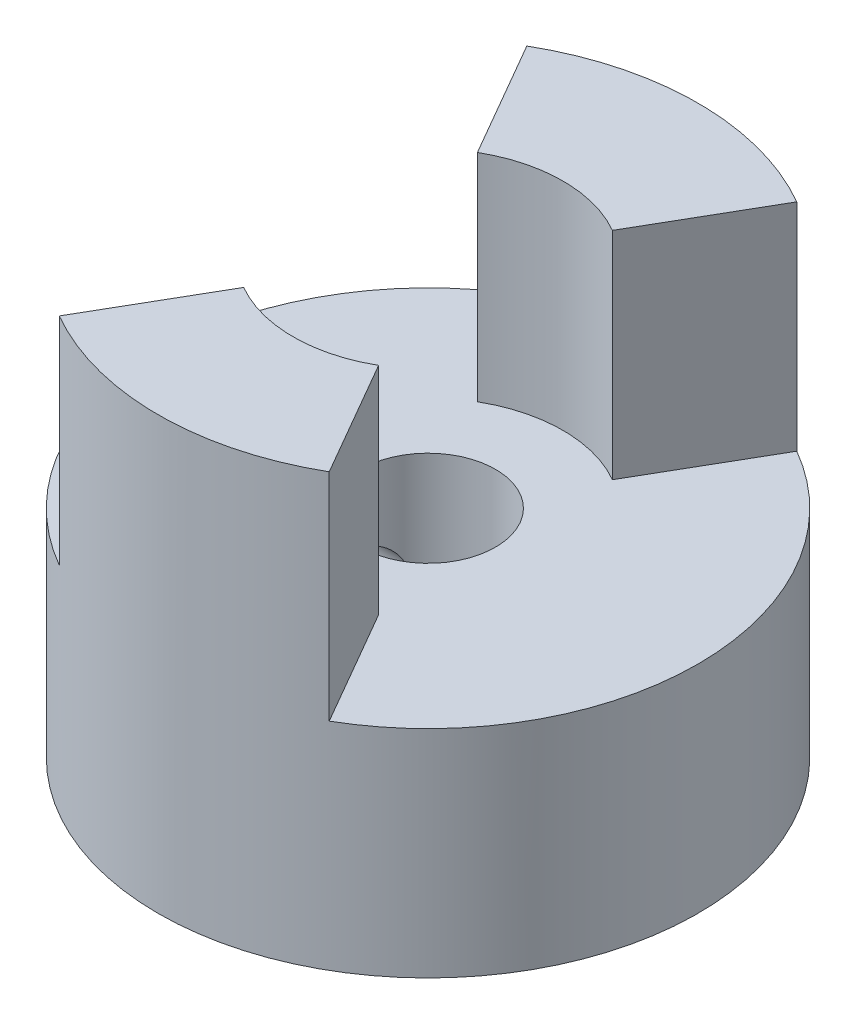
SolidWorks part; units mm, degrees
material "6061 Alloy"
ref_plane "Front Plane" through (0, 0, 0) normal (0, 0, 1) x (1, 0, 0)
ref_plane "Top Plane" through (0, 0, 0) normal (0, 1, 0) x (1, 0, 0)
ref_plane "Right Plane" through (0, 0, 0) normal (1, 0, 0) x (0, 0, -1)
sketch "Sketch1" plane through (0, 0, 0) normal (0, 1, 0) x (1, 0, 0)
  circle A0 centre (0, 0) radius 6.35
extrude "Boss-Extrude1" add sketch "Sketch1" along normal blind 10.16
hole_wizard "1/8 (0.125) Diameter Hole1" positions "Sketch2" profile "Sketch3" hole size "1/8" standard "ANSI Inch" end condition through all
sketch "Sketch2" plane through (0, 10.16, 0) normal (0, 1, 0) x (1, 0, 0)
  point P0 (0, 0)
sketch "Sketch3" plane through (0, 10.16, 0) normal (1, 0, 0) x (0, 0, 1)
  line L0 (0, 0) -> (0, 10.16)
  line L1 (0, 10.16) -> (1.5875, 10.16)
  line L2 (1.5875, 10.16) -> (1.5875, 0)
  line L5 (1.5875, 0) -> (0, 0)
  line L11 (0, -6.35) -> (0, 107.95) construction
  dimension "Thru Hole Dia." = 3.175
  dimension "Thru Hole Depth" = 10.16
sketch "Sketch4" plane through (0, 10.16, 0) normal (0, 1, 0) x (1, 0, 0)
  circle A0 centre (0, 0) radius 3.175
extrude "Cut-Extrude1" cut sketch "Sketch4" against normal blind 5.08
sketch "Sketch5" plane through (0, 10.16, 0) normal (0, 1, 0) x (1, 0, 0)
  line L0 (0, 0) -> (-7.62, -13.1982)
  line L1 (-7.62, -13.1982) -> (-7.62, 13.1982)
  line L2 (-7.62, 13.1982) -> (0, 0)
  line L3 (0, -55) -> (0, 55) construction
  dimension "D4" = 0
  dimension "D1" = 120
  dimension "D2" = 15.24
  dimension "D3" = 15.24
extrude "Cut-Extrude2" cut sketch "Sketch5" against normal blind 5.08
mirror "Mirror1" about plane through (0, 0, 0) normal (1, 0, 0) of "Cut-Extrude2"
hole_wizard "#2-56 Tapped Hole1" positions "3DSketch1" profile "Sketch6" tap size "#2-56" standard "ANSI Inch"
sketch3d "3DSketch1"
  point P0 (-6.35, 2.54, 0.0133)
  dimension "D1" = 2.54
sketch "Sketch6" plane through (-6.35, 2.54, 0.0133) normal (0, 1, 0) x (0.0021, 0, 1)
  line L0 (0, 0) -> (0, 4.7625)
  line L1 (0, 4.7625) -> (0.889, 4.7625)
  line L2 (0.889, 4.7625) -> (0.889, 0)
  line L5 (0.889, 0) -> (0, 0)
  line L11 (0, -6.35) -> (0, 107.95) construction
  dimension "Thru Tap Drill Dia." = 1.778
  dimension "Thru Tap Drill Depth" = 4.7625
cosmetic thread "Hole Thread1" parameters "D2"=2.1844
sketch "Sketch7" plane through (0, 0, 0) normal (1, 0, 0) x (0, 0, -1)
  circle A0 centre (0, 2.54) radius 1.0605
  dimension "D1" = 2.54
